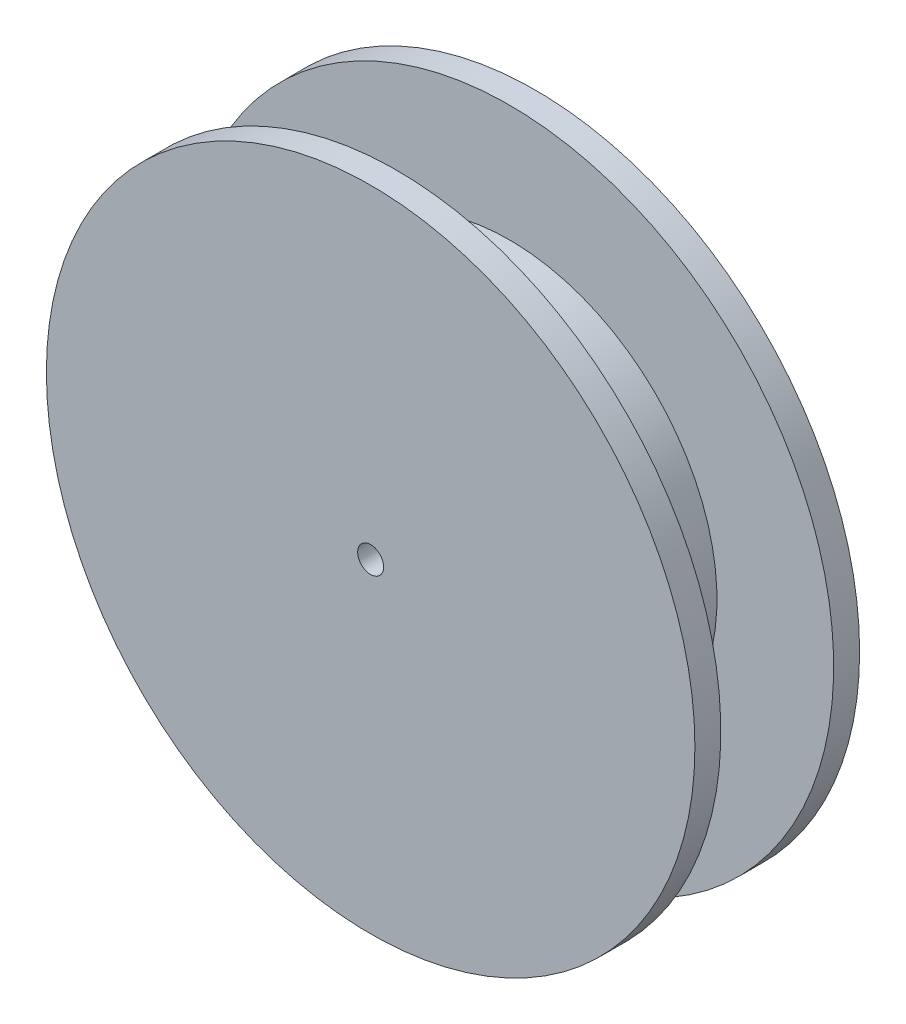
SolidWorks part; units mm, degrees
material "Brass"
ref_plane "Front Plane" through (0, 0, 0) normal (0, 0, 1) x (1, 0, 0)
ref_plane "Top Plane" through (0, 0, 0) normal (0, 1, 0) x (1, 0, 0)
ref_plane "Right Plane" through (0, 0, 0) normal (1, 0, 0) x (0, 0, -1)
sketch "Sketch1" plane through (0, 0, 0) normal (0, 0, 1) x (1, 0, 0)
  circle A0 centre (0, 0) radius 12.5
  circle A1 centre (0, 0) radius 0.5
  dimension "D1" = 25
  dimension "D2" = 1
extrude "Boss-Extrude1" add sketch "Sketch1" along normal blind 6.35
sketch "Sketch2" plane through (0, 0, 0) normal (1, 0, 0) x (0, 0, -1)
  line L0 (-5.35, 12.5) -> (-1, 12.5)
  line L1 (0, 12.5) -> (-6.35, 12.5) construction
  line L2 (-1, 12.5) -> (-1, 8)
  line L3 (-1, 8) -> (-5.35, 8)
  line L4 (-5.35, 8) -> (-5.35, 12.5)
  line L5 (0, 0) -> (-6.35, 0) construction
  line L6 (-6.35, 12.5) -> (-6.35, -12.5) construction
  line L7 (0, -12.5) -> (0, 12.5) construction
  dimension "D1" = 8
  dimension "D2" = 1
  dimension "D3" = 1
revolve "Cut-Revolve1" cut sketch "Sketch2" angle 360 about L5
